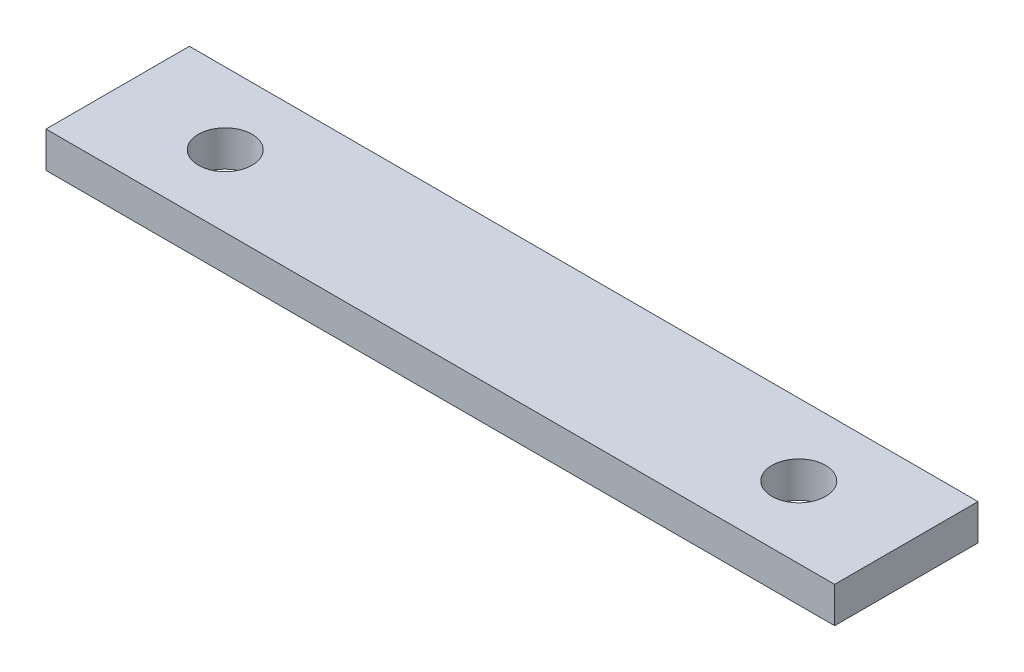
SolidWorks part; units mm, degrees
material "1060 Alloy"
ref_plane "Front Plane" through (0, 0, 0) normal (0, 0, 1) x (1, 0, 0)
ref_plane "Top Plane" through (0, 0, 0) normal (0, 1, 0) x (1, 0, 0)
ref_plane "Right Plane" through (0, 0, 0) normal (1, 0, 0) x (0, 0, -1)
sketch "Sketch1" plane through (0, 0, 0) normal (0, 1, 0) x (1, 0, 0)
  line L1 (-69.85, 12.7) -> (69.85, 12.7)
  line L2 (-69.85, 12.7) -> (-69.85, -12.7)
  line L3 (-69.85, -12.7) -> (69.85, -12.7)
  line L4 (69.85, 12.7) -> (69.85, -12.7)
  line L5 (-69.85, 12.7) -> (69.85, -12.7) construction
  line L6 (-69.85, -12.7) -> (69.85, 12.7) construction
  point P0 (0, 0)
  dimension "D1" = 25.4
  dimension "D2" = 139.7
extrude "Boss-Extrude1" add sketch "Sketch1" along normal mid plane 6.35
sketch "Sketch2" plane through (0, 3.175, 0) normal (0, 1, 0) x (1, 0, 0)
  line L1 (-50.8, 0) -> (50.8, 0)
  line L2 (-3.4925, 0) -> (3.4925, 0) construction
  circle A0 centre (50.8, 0) radius 4.7625
  circle A1 centre (-50.8, 0) radius 4.7625
  dimension "D2" = 9.525
  dimension "D1" = 101.6
extrude "Cut-Extrude1" cut sketch "Sketch2" against normal through all
sketch3d "TAG"
  line L0 (-69.85, 3.175, 12.7) -> (-69.85, -3.175, 12.7) construction
  line L1 (-69.85, 3.175, -12.7) -> (-69.85, 3.175, 12.7) construction
  line L2 (-69.85, 3.175, 12.7) -> (69.85, 3.175, 12.7) construction
  line L3 (-69.85, 3.175, 12.7) -> (-69.85, -3.175, 12.7)
  line L4 (-69.85, 3.175, -12.7) -> (-69.85, 3.175, 12.7)
  line L5 (-69.85, 3.175, 12.7) -> (69.85, 3.175, 12.7)
  dimension "D1" = 6.35
  dimension "D2" = 25.4
  dimension "D3" = 139.7
